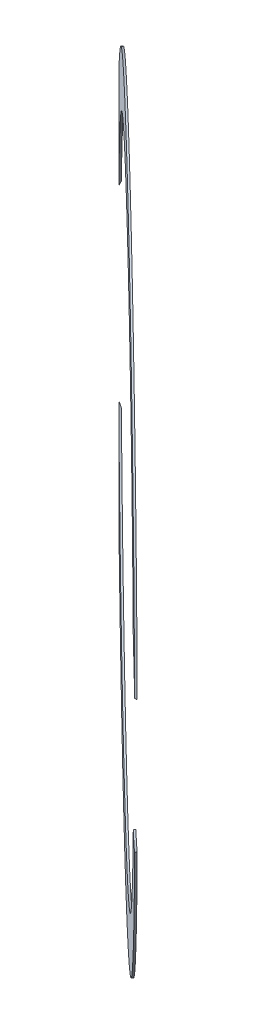
SolidWorks part; units mm, degrees
ref_plane "Front" through (0, 0, 0) normal (0, 0, 1) x (1, 0, 0)
ref_plane "Top" through (0, 0, 0) normal (0, 1, 0) x (1, 0, 0)
ref_plane "Right" through (0, 0, 0) normal (1, 0, 0) x (0, 0, -1)
sketch "Sketch2" plane through (-164.2276, 0, 170.5889) normal (-0.6935, 0, 0.7204) x (0.7204, 0, 0.6935)
  circle A0 centre (0, 0) radius 298.479
  circle A1 centre (0, 0) radius 257.204
  circle A2 centre (0, 0) radius 298.479 construction
  dimension "D1" = 41.275
  dimension "D2" = 596.958
extrude "Extrude1" add sketch "Sketch2" against normal blind 1.651
sketch "Sketch3" plane through (0, 0, 0) normal (0, 0, 1) x (1, 0, 0)
  circle A0 centre (0, 0) radius 76.2
  dimension "D1" = 152.4
extrude "Cut-Extrude1" cut sketch "Sketch3" along normal through all
sketch "Sketch4" plane through (0, 0, 0) normal (0, 0, 1) x (1, 0, 0)
  circle A0 centre (0, 0) radius 381
  dimension "D1" = 762
extrude "Cut-Extrude2" cut sketch "Sketch4" along normal blind 2.032 and the other way through all
split "Split1" bodies to split 105 106 resulting bodies 107 108
